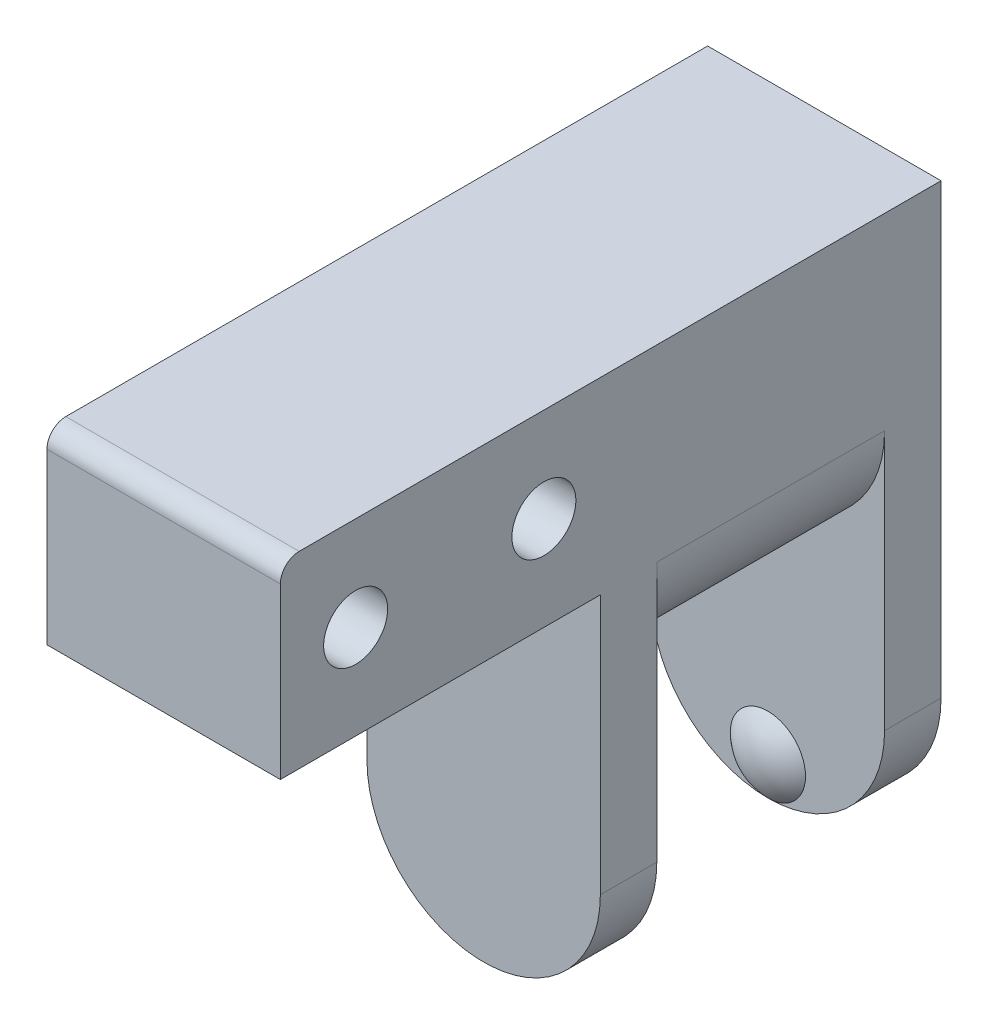
SolidWorks part; units mm, degrees
ref_plane "Спереди" through (0, 0, 0) normal (0, 0, 1) x (1, 0, 0)
ref_plane "Сверху" through (0, 0, 0) normal (0, 1, 0) x (1, 0, 0)
ref_plane "Справа" through (0, 0, 0) normal (1, 0, 0) x (0, 0, -1)
sketch "Эскиз2" plane through (0, 0, 0) normal (1, 0, 0) x (0, 0, -1)
  line L0 (12.1, -20) -> (15.1, -20)
  line L1 (15.1, -20) -> (15.1, 10)
  line L2 (15.1, 10) -> (-20, 10)
  line L3 (-20, 10) -> (-20, 0)
  line L4 (-20, 0) -> (-3, 0)
  line L5 (-3, 0) -> (-3, -20)
  line L6 (-3, -20) -> (0, -20)
  line L7 (0, -20) -> (0, 0)
  line L8 (0, 0) -> (12.1, 0)
  line L9 (12.1, 0) -> (12.1, -20)
  line L10 (0, -8) -> (12.1, -8)
  dimension "D1" = 30
  dimension "D2" = 20
  dimension "D3" = 3
  dimension "D4" = 12.1
  dimension "D5" = 8
  dimension "D6" = 10
  dimension "D7" = 20
extrude "Бобышка-Вытянуть1" add sketch "Эскиз2" along normal blind 12.4
sketch "Эскиз3" plane through (0, 0, 0) normal (0, 0, 1) x (1, 0, 0)
  line L0 (0, 0) -> (12.4, 0) construction
  line L1 (0, 0) -> (-4.3102, 0)
  line L2 (-4.3102, 0) -> (-4.3102, -10.1582)
  line L3 (-4.3102, -10.1582) -> (16.7843, -10.1582)
  line L4 (16.7843, -10.1582) -> (16.7843, 0)
  line L5 (16.7843, 0) -> (12.4, 0)
  arc A0 (0, 0) -> (12.4, 0) centre (6.2, 0) ccw
  dimension "D1" = 6.2
  dimension "D2" = 16.7843
  dimension "D3" = 4.3102
  dimension "D4" = 10.1582
extrude "Вырез-Вытянуть1" cut sketch "Эскиз3" against normal up to surface (12.1 mm away) up to face at (6.2, -14, -12.1)
sketch "Эскиз4" plane through (0, 0, 0) normal (0, 0, 1) x (1, 0, 0)
  line L0 (0, -13.8) -> (12.4, -13.8) construction
  line L1 (0, 0) -> (0, -20) construction
  line L2 (12.4, -20) -> (12.4, 0) construction
  line L3 (12.4, -20) -> (0, -20) construction
  line L4 (0, -13.8) -> (-4.5292, -13.8)
  line L5 (-4.5292, -13.8) -> (-4.5292, -23.0327)
  line L6 (-4.5292, -23.0327) -> (17.4573, -23.0327)
  line L7 (17.4573, -23.0327) -> (17.4573, -13.8)
  line L8 (17.4573, -13.8) -> (12.4, -13.8)
  arc A0 (0, -13.8) -> (12.4, -13.8) centre (6.2, -13.8) ccw
  dimension "D1" = 17.4573
  dimension "D2" = 4.5292
  dimension "D3" = 23.0327
extrude "Вырез-Вытянуть2" cut sketch "Эскиз4" against normal through all both and the other way through all
hole_wizard "Отверстие с зазором M31" [suppressed] positions "Эскиз7" profile "Эскиз8" hole size "M3" standard "IS"
sketch "Эскиз7" plane through (0, 7, 0) normal (0, 1, 0) x (1, 0, 0)
  line L0 (12.4, 0) -> (0, 0) construction
  line L1 (0, -20.1) -> (0, 0) construction
  point P0 (6.25, -10.05)
  dimension "D1" = 10.05
  dimension "D2" = 6.25
sketch "Эскиз8" plane through (6.25, 7, 10.05) normal (1, 0, 0) x (0, 0, 1)
  line L0 (0, 0) -> (0, 11.0215)
  line L1 (0, 11.0215) -> (1.7, 10)
  line L2 (1.7, 10) -> (1.7, 0)
  line L5 (1.7, 0) -> (0, 0)
  line L10 (0, 11.0215) -> (-1.7, 10) construction
  line L11 (0, -6.35) -> (0, 107.95) construction
  dimension "Диаметр отверстия" = 3.4
  dimension "Глубина отверстия" = 10
  dimension "Угол заточки сверла" = 118
fillet "Скругление1" [suppressed] radius 1
hole_wizard "Отверстие с зазором M32" positions "Эскиз10" profile "Эскиз11" hole size "M3" standard "IS"
sketch "Эскиз10" plane through (12.4, 0, 0) normal (1, 0, 0) x (0, 0, -1)
  line L0 (-20, 5) -> (0, 5) construction
  line L1 (-20, 10) -> (-20, 0) construction
  point P0 (-6, 5)
  point P2 (-16, 5)
  dimension "D1" = 4
  dimension "D2" = 6
  dimension "D3" = 20
sketch "Эскиз11" plane through (12.4, 5, 6) normal (0, 1, 0) x (0, 0, -1)
  line L0 (0, 0) -> (0, 16.0215)
  line L1 (0, 16.0215) -> (1.7, 15)
  line L2 (1.7, 15) -> (1.7, 0)
  line L5 (1.7, 0) -> (0, 0)
  line L10 (0, 16.0215) -> (-1.7, 15) construction
  line L11 (0, -6.35) -> (0, 107.95) construction
  dimension "Диаметр отверстия" = 3.4
  dimension "Глубина отверстия" = 15
  dimension "Угол заточки сверла" = 118
ref_plane "Плоскость1" through (6.2, 0, 0) normal (1, 0, 0) x (0, 0, -1)
sketch "Эскиз12" plane through (6.2, 0, 0) normal (1, 0, 0) x (0, 0, -1)
  line L0 (12.1, -20) -> (12.1, -18)
  line L1 (11.3, -18) -> (12.1, -18)
  arc A0 (12.1, -20) -> (11.3, -18) centre (14.2, -18) cw
  dimension "D1" = 0.8
  dimension "D2" = 2
revolve "Повернуть1" add sketch "Эскиз12" angle 360 about L1
fillet "Скругление2" radius 1 1 edges at (6.2, 10, 20)
